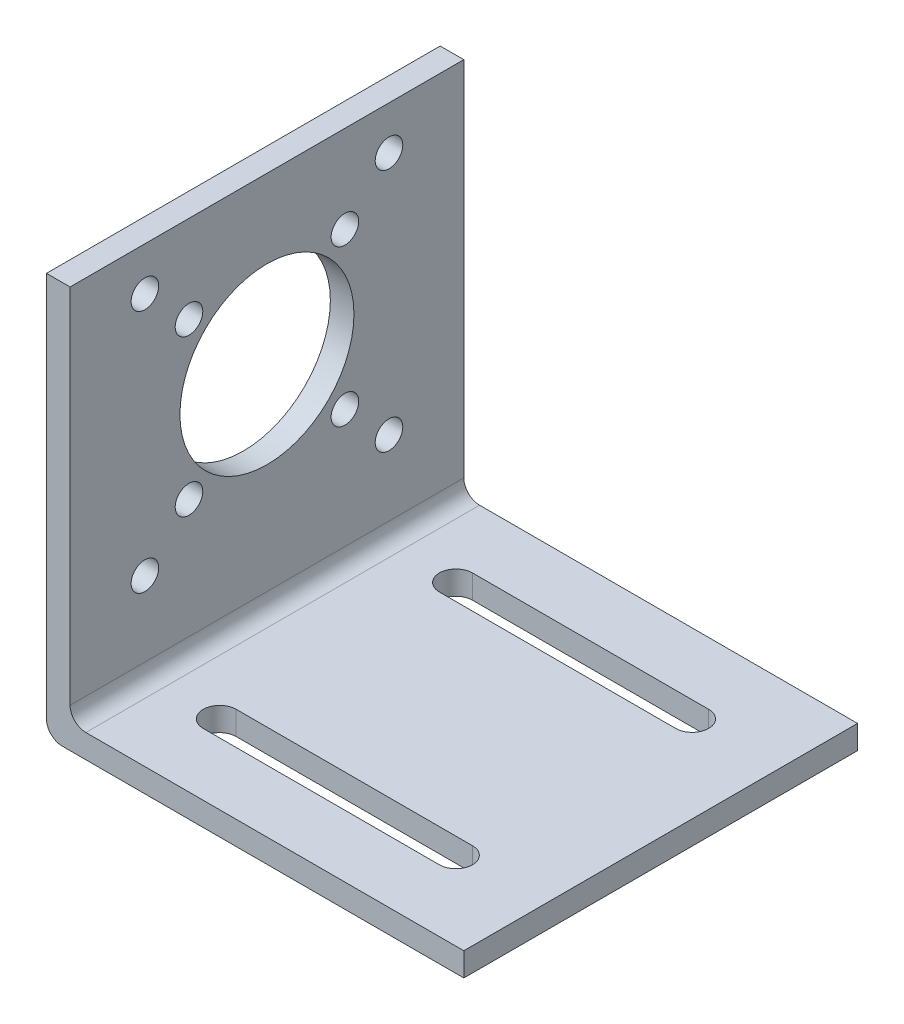
SolidWorks part; units mm, degrees
material "1060 Alloy"
ref_plane "Front" through (0, 0, 0) normal (0, 0, 1) x (1, 0, 0)
ref_plane "Top" through (0, 0, 0) normal (0, 1, 0) x (1, 0, 0)
ref_plane "Right" through (0, 0, 0) normal (1, 0, 0) x (0, 0, -1)
sketch "Sketch1" plane through (0, 0, 0) normal (0, 1, 0) x (1, 0, 0)
  line L1 (0, 0) -> (53, 0)
  line L2 (0, 0) -> (0, 50)
  line L3 (0, 50) -> (53, 50)
  line L4 (53, 0) -> (53, 50)
  dimension "D1" = 50
  dimension "D2" = 53
extrude "Boss-Extrude1" add sketch "Sketch1" along normal blind 3
sketch "Sketch2" plane through (0, 3, 0) normal (0, 1, 0) x (1, 0, 0)
  line L0 (53, 50) -> (0, 50) construction
  line L1 (0, 0) -> (3, 0)
  line L2 (0, 0) -> (0, 50)
  line L3 (0, 50) -> (3, 50)
  line L4 (3, 0) -> (3, 50)
  dimension "D1" = 3
extrude "Boss-Extrude2" add sketch "Sketch2" along normal blind 48
sketch "Sketch3" plane through (0, 3, 0) normal (0, 1, 0) x (1, 0, 0)
  line L0 (53, 0) -> (53, 50) construction
  line L1 (53, 0) -> (53, 50)
  line L2 (3, 0) -> (3, 50) construction
  line L3 (3, 0) -> (3, 50)
  line L4 (3, 25) -> (53, 25) construction
  line L5 (12, 40) -> (42, 40) construction
  line L6 (12, 42.1) -> (42, 42.1)
  line L7 (12, 37.9) -> (42, 37.9)
  line L8 (12, 10) -> (42, 10) construction
  line L9 (12, 7.9) -> (42, 7.9)
  line L10 (12, 12.1) -> (42, 12.1)
  arc A0 (12, 42.1) -> (12, 37.9) centre (12, 40) ccw
  arc A1 (42, 37.9) -> (42, 42.1) centre (42, 40) ccw
  arc A2 (12, 7.9) -> (12, 12.1) centre (12, 10) cw
  arc A3 (42, 12.1) -> (42, 7.9) centre (42, 10) cw
  point P8 (27, 40)
  point P15 (27, 10)
  dimension "D4" = 2.1
  dimension "D1" = 11
  dimension "D2" = 30
  dimension "D3" = 15
extrude "Cut-Extrude1" cut sketch "Sketch3" against normal through all contours L7 A1 L6 A0 | A3 L10 A2 L9
fillet "Fillet1" radius 2 2 edges at (3, 3, -25) (0, 0, -25)
sketch "Sketch4" plane through (3, 0, 0) normal (1, 0, 0) x (0, 0, -1)
  line L0 (0, 51) -> (0, 5) construction
  line L1 (0, 51) -> (0, 5)
  line L2 (0, 0) -> (50, 0) construction
  line L3 (0, 0) -> (50, 0)
  line L4 (25, 0) -> (25, 51) construction
  line L5 (0, 51) -> (50, 51) construction
  line L6 (25, 30) -> (50, 30) construction
  line L7 (50, 51) -> (50, 5) construction
  line L9 (9.5, 14.5) -> (40.5, 14.5) construction
  line L10 (9.5, 14.5) -> (9.5, 45.5) construction
  line L11 (9.5, 45.5) -> (40.5, 45.5) construction
  line L12 (40.5, 14.5) -> (40.5, 45.5) construction
  line L13 (9.5, 14.5) -> (40.5, 45.5) construction
  line L14 (9.5, 45.5) -> (40.5, 14.5) construction
  circle A0 centre (25, 30) radius 11.05
  circle A1 centre (25, 30) radius 14 construction
  circle A2 centre (34.899, 39.9) radius 1.75
  circle A6 centre (15.101, 39.9) radius 1.75
  circle A7 centre (15.101, 20.1) radius 1.75
  circle A8 centre (34.899, 20.1) radius 1.75
  circle A9 centre (9.5, 45.5) radius 1.75
  circle A10 centre (40.5, 45.5) radius 1.75
  circle A11 centre (9.5, 14.5) radius 1.75
  circle A12 centre (40.5, 14.5) radius 1.75
  dimension "D1" = 22.1
  dimension "D3" = 28
  dimension "D4" = 3.5
  dimension "D2" = 30
  dimension "D5" = 9.9
  dimension "D6" = 9.9
  dimension "D7" = 31
extrude "Cut-Extrude2" cut sketch "Sketch4" against normal through all contours A9 | A6 | A0 | A7 | A11 | A8 | A12 | A2 | A10
